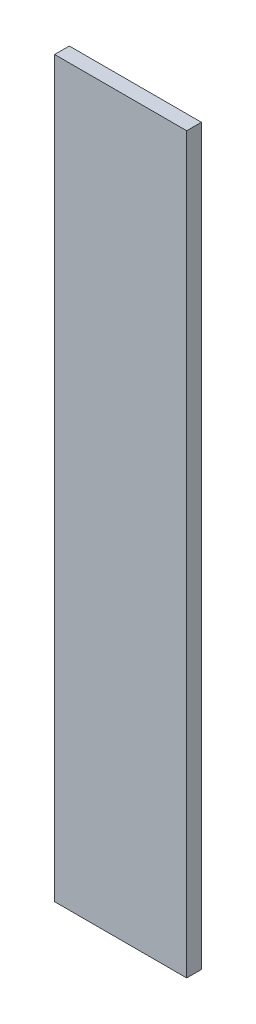
SolidWorks part; units mm, degrees
ref_plane "Plan de face" through (0, 0, 0) normal (0, 0, 1) x (1, 0, 0)
ref_plane "Plan de dessus" through (0, 0, 0) normal (0, 1, 0) x (1, 0, 0)
ref_plane "Plan de droite" through (0, 0, 0) normal (1, 0, 0) x (0, 0, -1)
sketch "Esquisse1" plane through (0, 0, 0) normal (0, 0, 1) x (1, 0, 0)
  line L1 (0, 0) -> (45, 0)
  line L2 (0, 0) -> (0, 250)
  line L3 (0, 250) -> (45, 250)
  line L4 (45, 0) -> (45, 250)
  dimension "D1" = 250
  dimension "D2" = 45
extrude "Boss.-Extru.1" add sketch "Esquisse1" along normal blind 5
